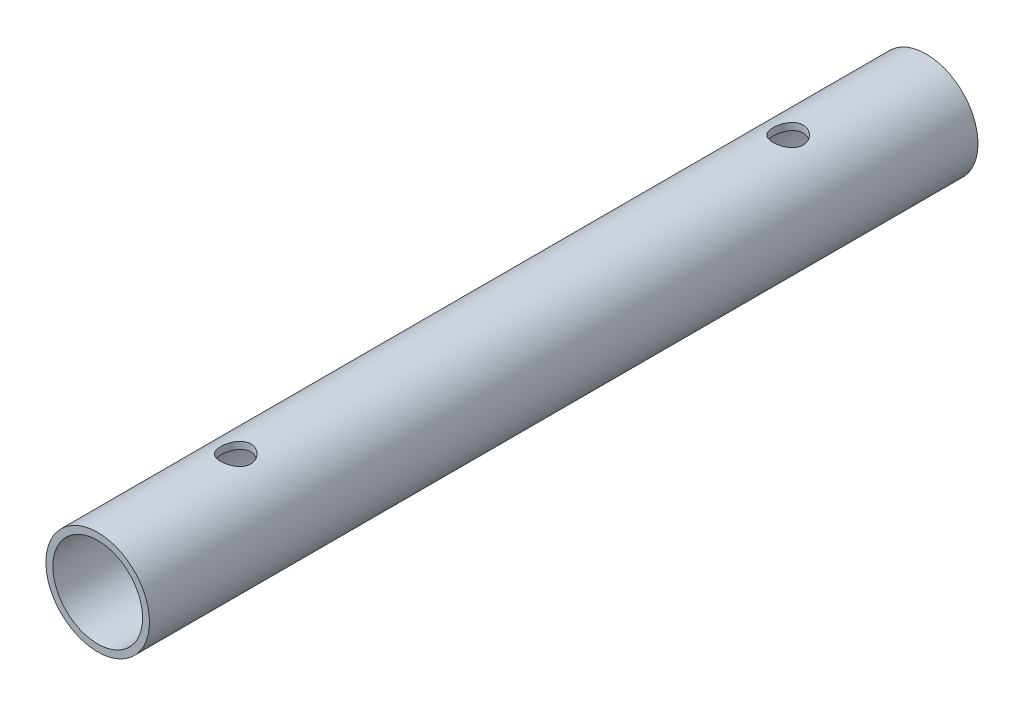
SolidWorks part; units mm, degrees
ref_plane "Front Plane" through (0, 0, 0) normal (0, 0, 1) x (1, 0, 0)
ref_plane "Top Plane" through (0, 0, 0) normal (0, 1, 0) x (1, 0, 0)
ref_plane "Right Plane" through (0, 0, 0) normal (1, 0, 0) x (0, 0, -1)
sketch "Sketch1" plane through (0, 0, 0) normal (0, 0, 1) x (1, 0, 0)
  circle A0 centre (0, 0) radius 19.05
  dimension "D1" = 38.1
extrude "Extrude-Thin1" add sketch "Sketch1" against normal up to surface (304.8 mm away) thin thin type one direction reverse wall 2.54
sketch "Sketch2" plane through (0, 0, 0) normal (0, 1, 0) x (1, 0, 0)
  line L0 (0, 50.8) -> (0, 0) construction
  line L1 (0, 304.8) -> (0, 254) construction
  line L2 (19.05, 304.8) -> (-19.05, 304.8) construction
  circle A0 centre (0, 50.8) radius 5.5563
  circle A1 centre (0, 254) radius 5.5562
  dimension "D1" = 11.1125
  dimension "D2" = 50.8
extrude "Cut-Extrude1" cut sketch "Sketch2" along normal through all
